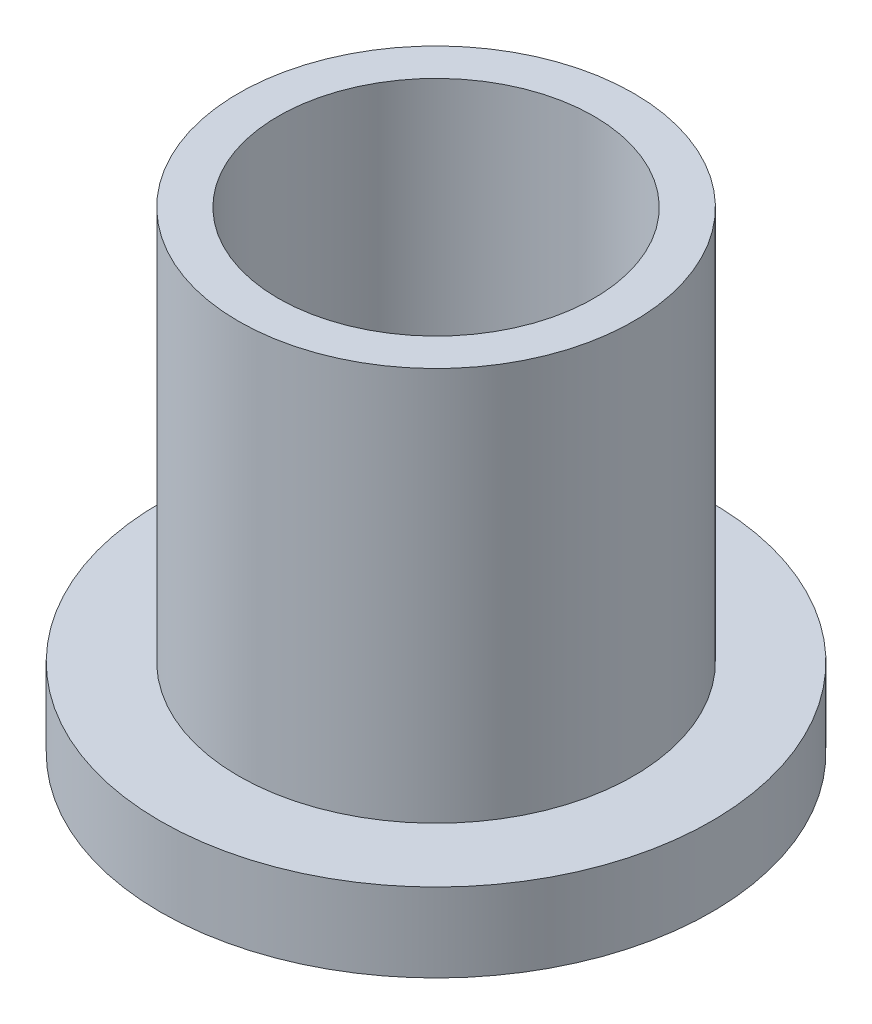
SolidWorks part; units mm, degrees
ref_plane "Front" through (0, 0, 0) normal (0, 0, 1) x (1, 0, 0)
ref_plane "Top" through (0, 0, 0) normal (0, 1, 0) x (1, 0, 0)
ref_plane "Right" through (0, 0, 0) normal (1, 0, 0) x (0, 0, -1)
sketch "Sketch1" plane through (0, 0, 0) normal (0, 1, 0) x (1, 0, 0)
  circle A0 centre (0, 0) radius 6.3627
  circle A1 centre (0, 0) radius 7.9629
  circle A2 centre (0, 0) radius 11.1125
  dimension "ID" = 12.7254
  dimension "OD" = 15.9258
  dimension "FlangeOD" = 22.225
sketch "Sketch2" plane through (0, 0, 0) normal (0, 1, 0) x (1, 0, 0)
  circle A0 centre (0, 0) radius 6.3627 construction
  circle A1 centre (0, 0) radius 7.9629 construction
  circle A2 centre (0, 0) radius 6.3627
  circle A3 centre (0, 0) radius 7.9629
extrude "Boss-Extrude1" add sketch "Sketch2" along normal blind 19.05
sketch "Sketch3" plane through (0, 0, 0) normal (0, 1, 0) x (1, 0, 0)
  circle A0 centre (0, 0) radius 11.1125 construction
  circle A1 centre (0, 0) radius 7.9629 construction
  circle A2 centre (0, 0) radius 11.1125
  circle A3 centre (0, 0) radius 7.9629
extrude "Boss-Extrude2" add sketch "Sketch3" along normal blind 3.175
